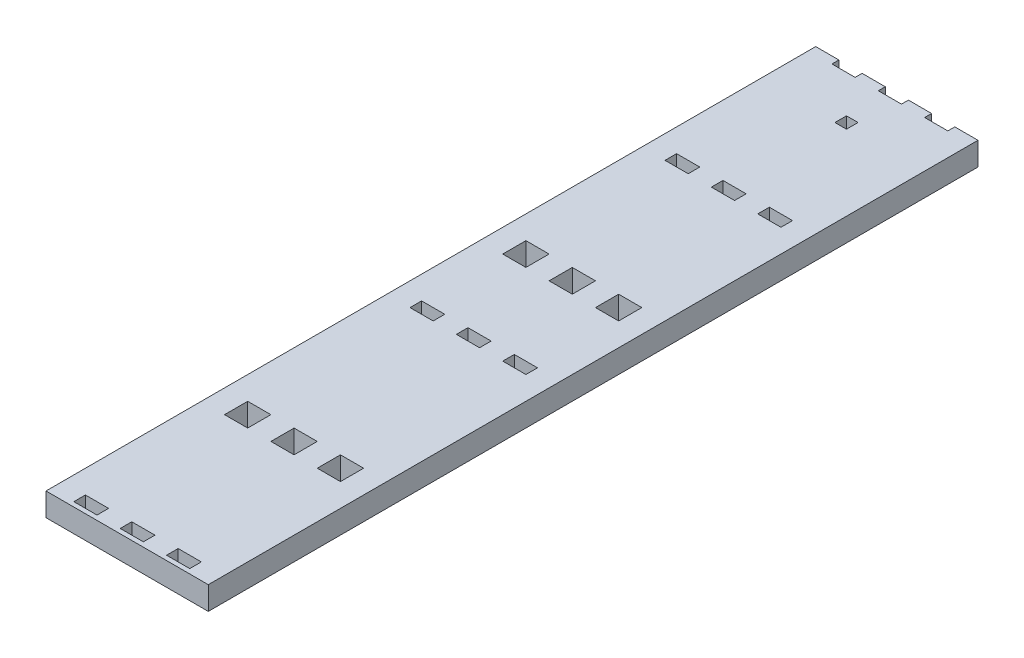
SolidWorks part; units mm, degrees
material "Balsa"
ref_plane "Plan de face" through (0, 0, 0) normal (0, 0, 1) x (1, 0, 0)
ref_plane "Plan de dessus" through (0, 0, 0) normal (0, 1, 0) x (1, 0, 0)
ref_plane "Plan de droite" through (0, 0, 0) normal (1, 0, 0) x (0, 0, -1)
sketch "Esquisse1" plane through (0, 0, 0) normal (0, 1, 0) x (1, 0, 0)
  line L1 (-42.9846, 44.6067) -> (27.0154, 44.6067)
  line L2 (-42.9846, 44.6067) -> (-42.9846, -287.3933)
  line L3 (-42.9846, -287.3933) -> (27.0154, -287.3933)
  line L4 (27.0154, 44.6067) -> (27.0154, -287.3933)
  dimension "D1" = 70
  dimension "D2" = 332
extrude "Boss.-Extru.1" add sketch "Esquisse1" along normal blind 10
sketch "Esquisse2" plane through (0, 10, 0) normal (0, 1, 0) x (1, 0, 0)
  line L1 (-32.9846, -217.3933) -> (-22.9846, -217.3933)
  line L2 (-32.9846, -217.3933) -> (-32.9846, -227.3933)
  line L3 (-32.9846, -227.3933) -> (-22.9846, -227.3933)
  line L4 (-22.9846, -217.3933) -> (-22.9846, -227.3933)
  line L5 (-42.9846, -287.3933) -> (27.0154, -287.3933) construction
  line L6 (-42.9846, 44.6067) -> (-42.9846, -287.3933) construction
  line L7 (-32.9846, -107.3933) -> (-22.9846, -107.3933)
  line L8 (-32.9846, -142.3933) -> (-22.9846, -142.3933)
  line L9 (-32.9846, -142.3933) -> (-32.9846, -147.3933)
  line L10 (-32.9846, -147.3933) -> (-22.9846, -147.3933)
  line L11 (-22.9846, -142.3933) -> (-22.9846, -147.3933)
  line L12 (-32.9846, -107.3933) -> (-32.9846, -97.3933)
  line L13 (-32.9846, -97.3933) -> (-22.9846, -97.3933)
  line L14 (-22.9846, -107.3933) -> (-22.9846, -97.3933)
  dimension "D1" = 10
  dimension "D2" = 10
  dimension "D3" = 60
  dimension "D4" = 10
  dimension "D5" = 140
  dimension "D6" = 5
  dimension "D7" = 10
  dimension "D8" = 10
  dimension "D9" = 10
  dimension "D10" = 10
  dimension "D11" = 10
  dimension "D12" = 180
extrude "Enlèv. mat.-Extru.1" cut sketch "Esquisse2" against normal blind 10
pattern_linear "Répétition linéaire1" count 3 spacing 20 along (1, 0, 0) of "Enlèv. mat.-Extru.1"
sketch "Esquisse4" plane through (0, 10, 0) normal (0, 1, 0) x (1, 0, 0)
  line L0 (-42.9846, 44.6067) -> (-42.9846, -287.3933) construction
  line L1 (-42.9846, -287.3933) -> (-32.9846, -287.3933)
  line L2 (-42.9846, -287.3933) -> (-42.9846, -292.3933)
  line L3 (-42.9846, -292.3933) -> (-32.9846, -292.3933)
  line L4 (-32.9846, -287.3933) -> (-32.9846, -292.3933)
  line L5 (-42.9846, 44.6067) -> (-32.9846, 44.6067)
  line L6 (-42.9846, 44.6067) -> (-42.9846, 47.6067)
  line L7 (-42.9846, 47.6067) -> (-32.9846, 47.6067)
  line L8 (-32.9846, 44.6067) -> (-32.9846, 47.6067)
  line L9 (27.0154, 44.6067) -> (-42.9846, 44.6067) construction
  line L10 (-42.9846, -287.3933) -> (27.0154, -287.3933) construction
  dimension "D1" = 10
  dimension "D2" = 3
  dimension "D3" = 5
  dimension "D4" = 10
  dimension "D5" = 0
  dimension "D6" = 0
  dimension "D7" = 0
  dimension "D8" = 0
extrude "Boss.-Extru.2" add sketch "Esquisse4" against normal blind 10
pattern_linear "Répétition linéaire2" count 4 spacing 20 along (1, 0, 0) of "Boss.-Extru.2"
sketch "Esquisse12" plane through (0, 10, 0) normal (0, 1, 0) x (1, 0, 0)
  line L1 (-32.9846, -37.3933) -> (-22.9846, -37.3933)
  line L2 (-32.9846, -37.3933) -> (-32.9846, -32.3933)
  line L3 (-32.9846, -32.3933) -> (-22.9846, -32.3933)
  line L4 (-22.9846, -37.3933) -> (-22.9846, -32.3933)
  line L6 (-32.9846, -287.3933) -> (-22.9846, -287.3933) construction
  line L7 (-42.9846, 47.6067) -> (-42.9846, -292.3933) construction
  dimension "D1" = 250
  dimension "D2" = 5
  dimension "D3" = 10
  dimension "D4" = 10
extrude "Enlèv. mat.-Extru.7" cut sketch "Esquisse12" against normal blind 10
pattern_linear "Répétition linéaire5" count 3 spacing 20 along (1, 0, 0) of "Enlèv. mat.-Extru.7"
sketch "Esquisse14" plane through (0, 10, 0) normal (0, 1, 0) x (1, 0, 0)
  line L1 (-42.9846, -292.3933) -> (27.0154, -292.3933)
  line L2 (-42.9846, -292.3933) -> (-42.9846, -294.3933)
  line L3 (-42.9846, -294.3933) -> (27.0154, -294.3933)
  line L4 (27.0154, -292.3933) -> (27.0154, -294.3933)
  dimension "D1" = 70
  dimension "D2" = 2
extrude "Boss.-Extru.4" add sketch "Esquisse14" against normal blind 10
sketch "Esquisse17" plane through (0, 0, -44.6067) normal (0, 0, -1) x (-1, 0, 0)
  line L1 (32.9846, 0) -> (22.9846, 0)
  line L2 (32.9846, 0) -> (32.9846, 10)
  line L3 (32.9846, 10) -> (22.9846, 10)
  line L4 (22.9846, 0) -> (22.9846, 10)
  line L5 (12.9846, 0) -> (2.9846, 0)
  line L6 (12.9846, 0) -> (12.9846, 10)
  line L7 (12.9846, 10) -> (2.9846, 10)
  line L8 (2.9846, 0) -> (2.9846, 10)
  line L9 (-7.0154, 0) -> (-17.0154, 0)
  line L10 (-7.0154, 0) -> (-7.0154, 10)
  line L11 (-7.0154, 10) -> (-17.0154, 10)
  line L12 (-17.0154, 0) -> (-17.0154, 10)
extrude "Enlèv. mat.-Extru.10" cut sketch "Esquisse17" against normal blind 10
sketch "Esquisse18" plane through (0, 0, -47.6067) normal (0, 0, -1) x (-1, 0, 0)
  line L1 (42.9846, 0) -> (32.9846, 0)
  line L2 (42.9846, 0) -> (42.9846, 10)
  line L3 (42.9846, 10) -> (32.9846, 10)
  line L4 (32.9846, 0) -> (32.9846, 10)
  line L5 (22.9846, 0) -> (12.9846, 0)
  line L6 (22.9846, 0) -> (22.9846, 10)
  line L7 (22.9846, 10) -> (12.9846, 10)
  line L8 (12.9846, 0) -> (12.9846, 10)
  line L9 (2.9846, 0) -> (-7.0154, 0)
  line L10 (2.9846, 0) -> (2.9846, 10)
  line L11 (2.9846, 10) -> (-7.0154, 10)
  line L12 (-7.0154, 0) -> (-7.0154, 10)
  line L13 (-17.0154, 0) -> (-27.0154, 0)
  line L14 (-17.0154, 0) -> (-17.0154, 10)
  line L15 (-17.0154, 10) -> (-27.0154, 10)
  line L16 (-27.0154, 0) -> (-27.0154, 10)
extrude "Enlèv. mat.-Extru.11" cut sketch "Esquisse18" against normal blind 10
sketch "Esquisse19" plane through (0, 10, 0) normal (0, 1, 0) x (1, 0, 0)
  line L0 (-12.9846, 34.6067) -> (-2.9846, 34.6067) construction
  line L1 (-10.4846, 13.3767) -> (-5.4846, 13.3767)
  line L2 (-10.4846, 13.3767) -> (-10.4846, 18.3767)
  line L3 (-10.4846, 18.3767) -> (-5.4846, 18.3767)
  line L4 (-5.4846, 13.3767) -> (-5.4846, 18.3767)
  line L5 (-42.9846, 37.6067) -> (-42.9846, -294.3933) construction
  dimension "D1" = 16.23
  dimension "D2" = 5
  dimension "D3" = 5
  dimension "D4" = 32.5
extrude "Enlèv. mat.-Extru.12" cut sketch "Esquisse19" against normal blind 10
